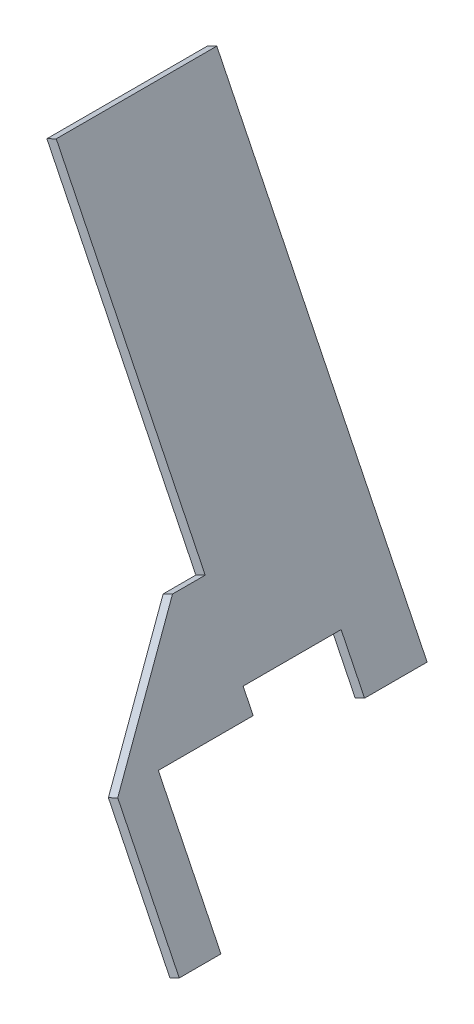
SolidWorks part; units mm, degrees
ref_plane "Front Plane" through (0, 0, 0) normal (0, 0, 1) x (1, 0, 0)
ref_plane "Top Plane" through (0, 0, 0) normal (0, 1, 0) x (1, 0, 0)
ref_plane "Right Plane" through (0, 0, 0) normal (1, 0, 0) x (0, 0, -1)
sketch "Sketch2" plane through (0, 0, 116.7919) normal (0, 0, 1) x (1, 0, 0)
  line L0 (-1177.6518, 1643.98) -> (-1173.1637, 1646.184)
  line L1 (-1177.6518, 1643.98) -> (-1046.4331, 1376.7681)
  line L2 (-1173.1637, 1646.184) -> (-1041.945, 1378.972)
  line L3 (-1046.4331, 1376.7681) -> (-1041.945, 1378.972)
  line L5 (-1030.2949, 1343.9045) -> (-1199.1162, 1687.6899) construction
  line L7 (-1025.8068, 1346.1084) -> (-1194.6281, 1689.8938) construction
extrude "Boss-Extrude1" add sketch "Sketch2" along normal up to surface (210.2958 mm away)
ref_plane "Plane1" through (-293.905, -144.3267, 0) normal (0.8976, 0.4408, 0) x (-0.4408, 0.8976, 0)
sketch "Sketch5" plane through (-293.905, -144.3267, 0) normal (-0.8976, -0.4408, 0) x (0, 0, 1)
  line L5 (327.0878, 1994.7492) -> (327.0878, 1697.0571) construction
  line L10 (327.0878, 1994.7492) -> (116.7919, 1994.7492) construction
  line L12 (132.4795, 1831.6775) -> (116.7919, 1831.6775)
  line L13 (116.7919, 1779.4837) -> (162.2919, 1779.4837)
  line L14 (116.7919, 1779.4837) -> (116.7919, 1623.4341)
  line L15 (116.7919, 1623.4341) -> (327.0878, 1623.4341)
  line L16 (327.0878, 1994.7492) -> (327.0878, 1623.4341)
  line L17 (167.2919, 1715.6885) -> (167.2919, 1769.4837) construction
  line L18 (327.0878, 1994.7492) -> (116.7919, 1994.7492)
  line L19 (177.2919, 1769.4837) -> (177.2919, 1715.6885) construction
  line L20 (39.7919, 1769.4837) -> (49.7919, 1769.4837) construction
  line L21 (162.2919, 1779.4837) -> (162.2919, 1711.3276)
  line L22 (162.2919, 1711.3276) -> (182.2919, 1711.3276)
  line L23 (182.2919, 1711.3276) -> (182.2919, 1778.2602)
  line L25 (132.4795, 1831.6775) -> (182.2919, 1778.2602)
  line L27 (116.7919, 1831.6775) -> (116.7919, 1994.7492)
  line L28 (116.7919, 1994.7492) -> (116.7919, 1697.0571) construction
  line L29 (131.3652, 1832.8725) -> (51.5676, 1918.4449) construction
  dimension "D1" = 10
  dimension "D2" = 156.0496
  dimension "D3" = 5
  dimension "D4" = 5
  dimension "D5" = 132.4795
  dimension "D6" = 1711.3276
extrude "Cut-Extrude3" cut sketch "Sketch5" along normal through all
sketch "Sketch6" plane through (0, 0, 116.7919) normal (0, 0, -1) x (-1, 0, 0)
  line L0 (1087.5971, 1460.594) -> (1083.1091, 1462.798)
  line L1 (1087.5971, 1460.594) -> (1177.2188, 1643.0983)
  line L2 (1083.1091, 1462.798) -> (1172.7307, 1645.3023)
  line L3 (1177.2188, 1643.0983) -> (1172.7307, 1645.3023)
  line L4 (1025.8068, 1346.1084) -> (1194.6281, 1689.8938) construction
  line L5 (1030.2949, 1343.9045) -> (1199.1162, 1687.6899) construction
  line L8 (1087.5971, 1460.594) -> (1199.7986, 1405.4957) construction
  line L9 (1082.5751, 1596.0272) -> (1185.1849, 1647.0603) construction
extrude "Boss-Extrude2" add sketch "Sketch6" along normal up to surface (77 mm away)
sketch "Sketch7" plane through (-789.2041, 1607.1247, 0) normal (0.4408, -0.8976, 0) x (0.8976, 0.4408, 0)
  line L0 (-327.4299, 69.7919) -> (-332.4299, 69.7919)
  line L1 (-327.4299, 69.7919) -> (-327.4299, 39.7919)
  line L2 (-332.4299, 69.7919) -> (-332.4299, 39.7919)
  line L3 (-327.4299, 39.7919) -> (-332.4299, 39.7919)
  line L4 (-327.4299, 39.7919) -> (-327.4299, 116.7919) construction
  line L5 (-332.4299, 39.7919) -> (-332.4299, 116.7919) construction
  line L6 (-332.4299, 39.7919) -> (-327.4299, 39.7919) construction
  dimension "D1" = 30
extrude "Boss-Extrude4" add sketch "Sketch7" along normal blind 25.5
